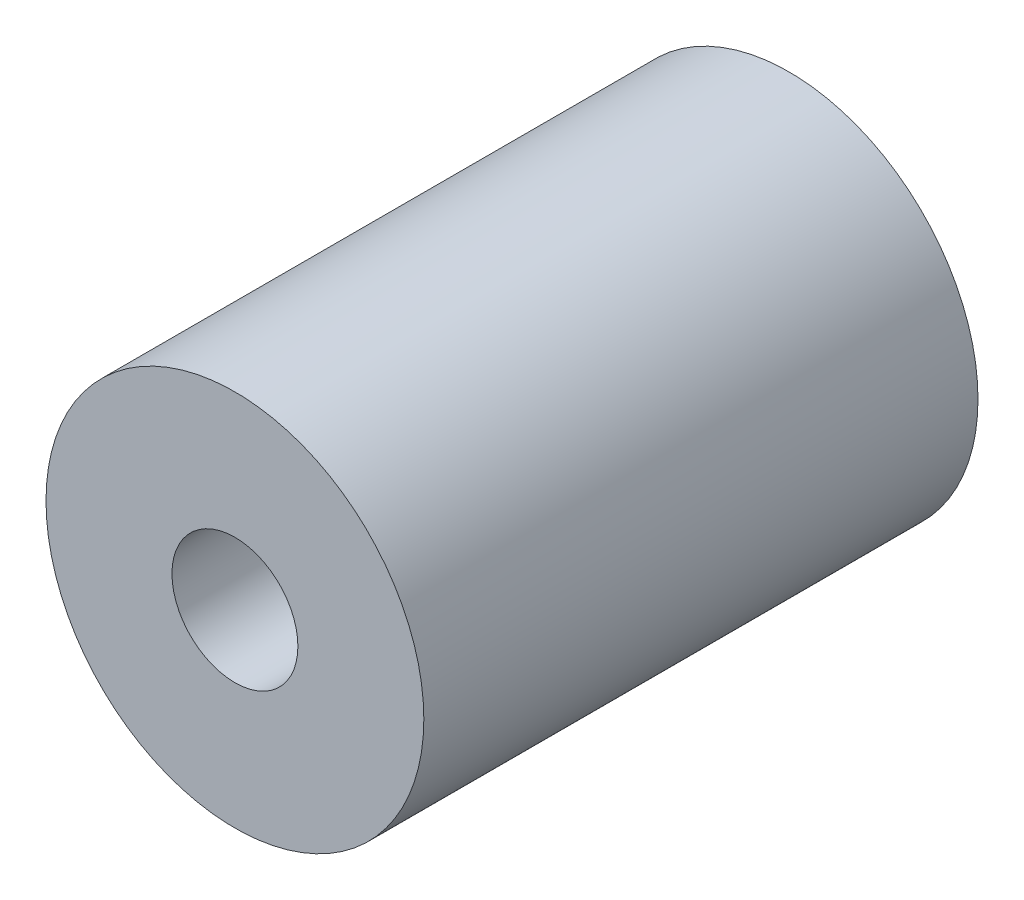
SolidWorks part; units mm, degrees
ref_plane "Front Plane" through (0, 0, 0) normal (0, 0, 1) x (1, 0, 0)
ref_plane "Top Plane" through (0, 0, 0) normal (0, 1, 0) x (1, 0, 0)
ref_plane "Right Plane" through (0, 0, 0) normal (1, 0, 0) x (0, 0, -1)
sketch "Sketch1" plane through (0, 0, 0) normal (0, 0, 1) x (1, 0, 0)
  circle A0 centre (0, 0) radius 9.525
  circle A1 centre (0, 0) radius 3.175
  dimension "D1" = 19.05
  dimension "D2" = 6.35
extrude "Boss-Extrude1" add sketch "Sketch1" along normal blind 27.94
sketch "Sketch2" plane through (0, 0, 0) normal (0, 0, -1) x (-1, 0, 0)
  circle A0 centre (0, 0) radius 4.7625
  circle A1 centre (0, 0) radius 3.175 construction
  circle A2 centre (0, 0) radius 9.525
  circle A3 centre (0, 0) radius 9.525
  circle A4 centre (0, 0) radius 3.175
  circle M4 centre (0, 0) radius 3.175
  dimension "D1" = 9.525
  dimension "D2" = 0
extrude "Cut-Extrude1" cut sketch "Sketch2" against normal blind 6.5024 contours A0 M4
